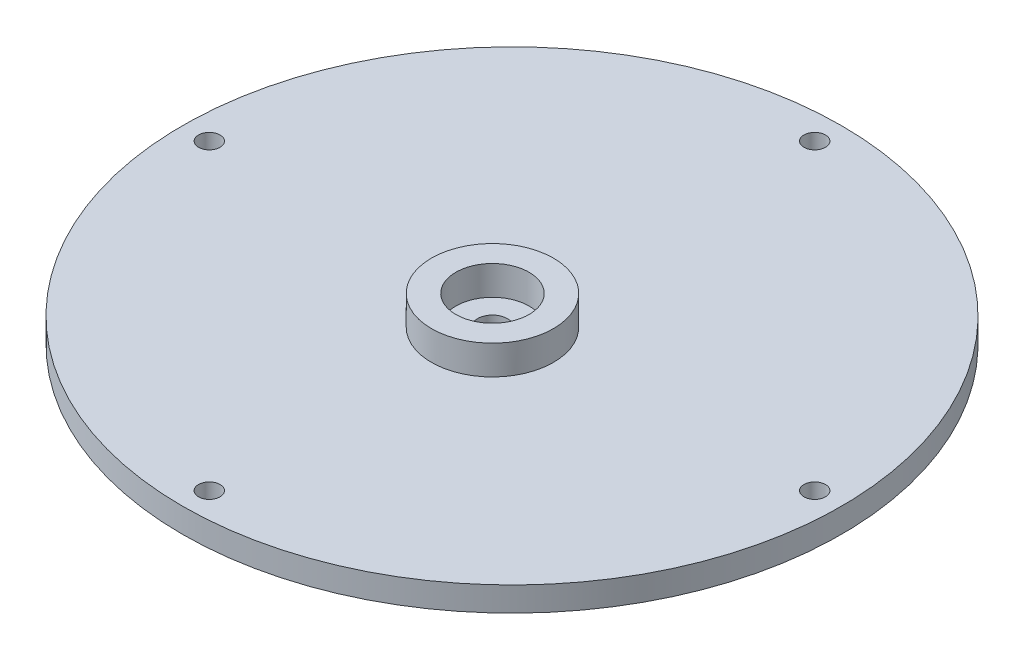
SolidWorks part; units mm, degrees
material "Acrylic (Medium-high impact)"
ref_plane "Front Plane" through (0, 0, 0) normal (0, 0, 1) x (1, 0, 0)
ref_plane "Top Plane" through (0, 0, 0) normal (0, 1, 0) x (1, 0, 0)
ref_plane "Right Plane" through (0, 0, 0) normal (1, 0, 0) x (0, 0, -1)
sketch "Sketch1" plane through (0, 0, 0) normal (0, 0, 1) x (1, 0, 0)
  line L0 (0, 0) -> (-67.5, 0)
  line L1 (-67.5, 0) -> (-67.5, -5)
  line L2 (-67.5, -5) -> (-50, -5)
  line L3 (-50, -5) -> (-50, -10)
  line L7 (0, -10) -> (0, 0)
  line L8 (-50, -10) -> (0, -10)
  dimension "D1" = 67.5
  dimension "D2" = 50
  dimension "D3" = 5
  dimension "D4" = 5
revolve "Revolve1" add sketch "Sketch1" angle 360 about L7
sketch "Sketch2" plane through (0, 0, 0) normal (0, 1, 0) x (1, 0, 0)
  line L0 (0, 0) -> (0, -4) construction
  circle A0 centre (0, -4) radius 7.5
  circle A1 centre (0, -4) radius 12.5
  dimension "D2" = 15
  dimension "D3" = 25
  dimension "D1" = 4
extrude "Boss-Extrude1" add sketch "Sketch2" along normal blind 6
sketch "Sketch3" plane through (0, -10, 0) normal (0, -1, 0) x (1, 0, 0)
  line L0 (0, 4) -> (0, 0) construction
  circle A0 centre (0, 4) radius 10.5
  dimension "D2" = 21
  dimension "D1" = 4
extrude "Cut-Extrude1" cut sketch "Sketch3" against normal blind 3
sketch "Sketch4" plane through (0, 0, 0) normal (0, 1, 0) x (1, 0, 0)
  circle A0 centre (0, -4) radius 3.05
  dimension "D1" = 6.1
extrude "Cut-Extrude2" cut sketch "Sketch4" against normal through all
sketch "Sketch5" plane through (0, 0, 0) normal (0, 1, 0) x (1, 0, 0)
  line L0 (0, 0) -> (0, 67.5) construction
  circle A0 centre (0, 0) radius 67.5 construction
  circle A1 centre (0, 62) radius 2.2
  circle A2 centre (62, 0) radius 2.2
  circle A3 centre (0, -62) radius 2.2
  circle A4 centre (-62, 0) radius 2.2
  point P17 (0, 0)
  dimension "D1" = 4.4
  dimension "D2" = 62
  dimension "D3" = 4
extrude "Cut-Extrude3" cut sketch "Sketch5" against normal through all
sketch "Sketch6" plane through (0, -5, 0) normal (0, -1, 0) x (1, 0, 0)
  circle A0 centre (0, 0) radius 57
  circle A1 centre (0, 0) radius 54
  dimension "D1" = 114
  dimension "D2" = 108
extrude "Cut-Extrude4" cut sketch "Sketch6" against normal blind 2
